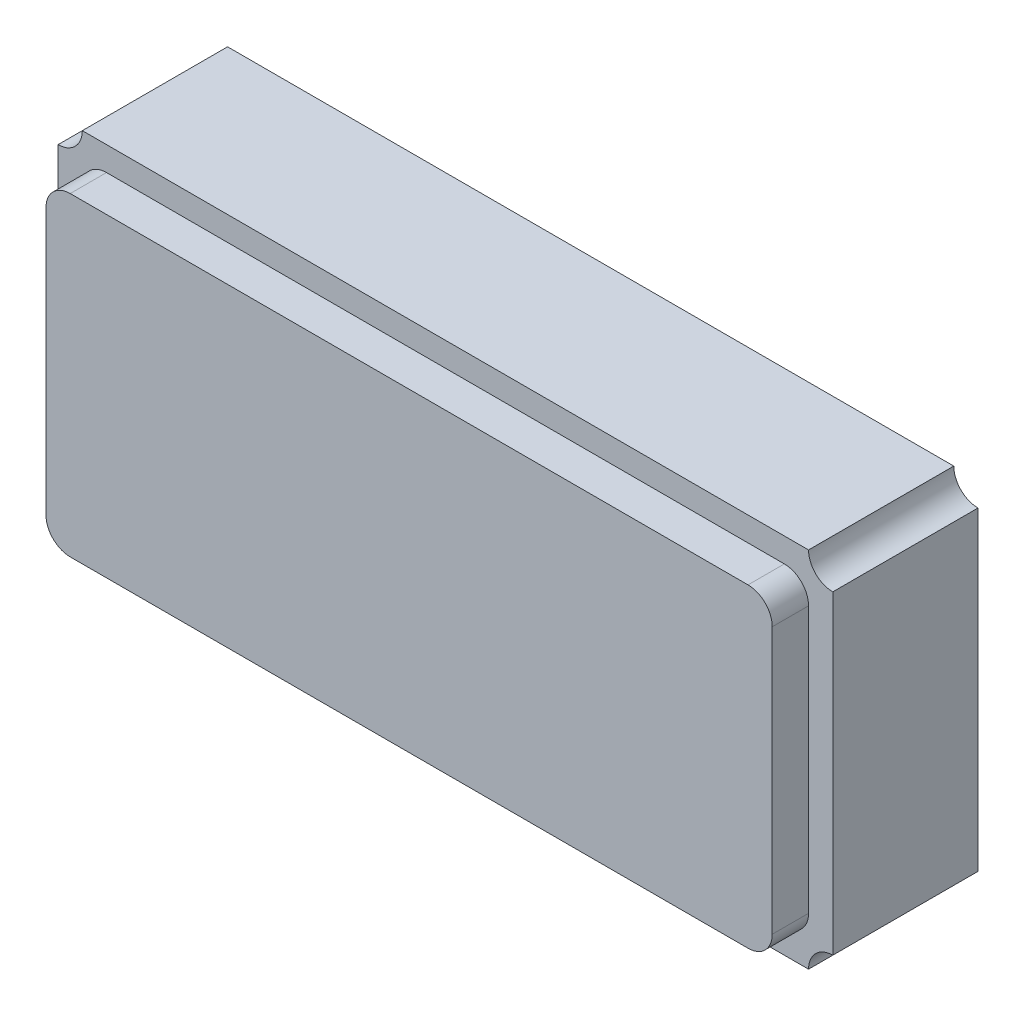
SolidWorks part; units mm, degrees
ref_plane "Front Plane" through (0, 0, 0) normal (0, 0, 1) x (1, 0, 0)
ref_plane "Top Plane" through (0, 0, 0) normal (0, 1, 0) x (1, 0, 0)
ref_plane "Right Plane" through (0, 0, 0) normal (1, 0, 0) x (0, 0, -1)
sketch "Sketch1" plane through (0, 0, 0) normal (0, 0, 1) x (1, 0, 0)
  line L0 (0.1, 0) -> (0, 0) construction
  line L1 (0.1, 0) -> (3.1, 0)
  line L2 (0, 0.1) -> (0, 1.4)
  line L3 (0.1, 1.5) -> (3.1, 1.5)
  line L4 (3.2, 0) -> (3.2, 0.1) construction
  line L5 (0, 0) -> (0, 0.1) construction
  line L6 (0, 0.75) -> (3.2, 0.75) construction
  line L7 (0, 1.4) -> (0, 1.5) construction
  line L8 (1.6, 1.5) -> (1.6, 0) construction
  line L9 (0, 1.5) -> (0.1, 1.5) construction
  line L10 (3.1, 1.5) -> (3.2, 1.5) construction
  line L11 (3.2, 1.5) -> (3.2, 1.4) construction
  line L13 (3.2, 0) -> (3.1, 0) construction
  line L14 (3.2, 0.1) -> (3.2, 1.4)
  arc A0 (0.1, 1.5) -> (0, 1.4) centre (0, 1.5) cw
  arc A1 (0.1, 0) -> (0, 0.1) centre (0, 0) ccw
  arc A2 (3.1, 0) -> (3.2, 0.1) centre (3.2, 0) cw
  arc A3 (3.2, 1.4) -> (3.1, 1.5) centre (3.2, 1.5) cw
  point P15 (1.6, 0)
  dimension "D3" = 0.1
  dimension "D1" = 1.5
  dimension "D2" = 3.2
  dimension "D4" = 1.3
extrude "Boss-Extrude1" add sketch "Sketch1" along normal blind 0.6
sketch "Sketch2" plane through (0, 0, 0.6) normal (0, 0, 1) x (1, 0, 0)
  line L0 (0, 0.75) -> (3.2, 0.75) construction
  line L1 (0, 1.4) -> (0, 0.1) construction
  line L4 (3.1, 1.5) -> (0.1, 1.5) construction
  line L5 (1.6, 1.5) -> (1.6, 0) construction
  line L6 (0.1, 0) -> (3.1, 0) construction
  line L7 (0.1, 1.4) -> (3.1, 1.4)
  line L8 (0.1, 1.4) -> (0.1, 0.1)
  line L9 (0.1, 0.1) -> (3.1, 0.1)
  line L10 (3.1, 1.4) -> (3.1, 0.1)
  point P16 (1.6, 1.4)
  point P17 (3.1, 0.75)
  dimension "D1" = 3
  dimension "D2" = 1.3
extrude "Boss-Extrude2" add sketch "Sketch2" along normal blind 0.15
fillet "Fillet1" radius 0.1 4 edges at (3.1, 1.4, 0.675) (0.1, 1.4, 0.675) (0.1, 0.1, 0.675) (3.1, 0.1, 0.675)
